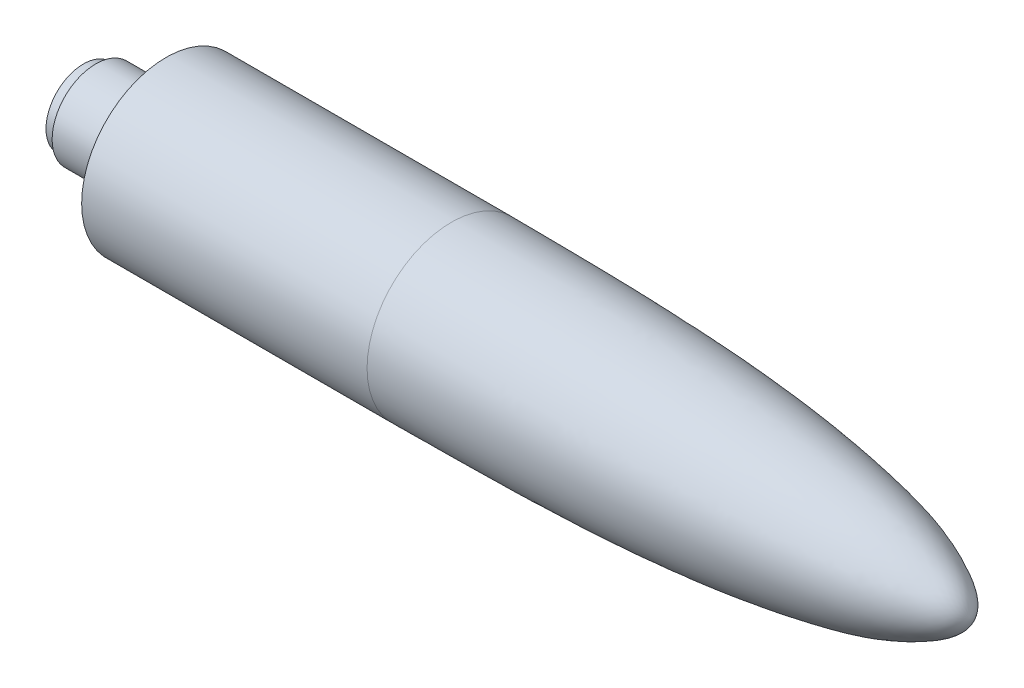
SolidWorks part; units mm, degrees
ref_plane "Front Plane" through (0, 0, 0) normal (0, 0, 1) x (1, 0, 0)
ref_plane "Top Plane" through (0, 0, 0) normal (0, 1, 0) x (1, 0, 0)
ref_plane "Right Plane" through (0, 0, 0) normal (1, 0, 0) x (0, 0, -1)
sketch "Sketch1" plane through (0, 0, 0) normal (0, 1, 0) x (1, 0, 0)
  line L0 (-27.2913, -6.7793) -> (4.4002, -6.7738) construction
  line L1 (0, 0) -> (57.2, 0) construction
  line L2 (0, 0) -> (0, -6)
  line L3 (0, -6) -> (20.3, -6)
  line L4 (0, 0) -> (0, 6) construction
  line L5 (0, 6) -> (20.3, 6) construction
  line L6 (57.2, 0) -> (57.0631, 6.2921) construction
  line L7 (0, 0) -> (57.2, 0)
  spline S0 degree 3 poles (20.3, -6) (29.6375, -5.9369) (42.0157, -5.942) (53.9398, -3.0181) (57.01, -1.0472) (57.2015, -0.0702) (57.2, 0) knots 0 0 0 0 0.749117 0.922481 0.994604 1 1 1 1
  dimension "D1" = 57.2
  dimension "D2" = 6
  dimension "D3" = 20.3
  dimension "D4" = 6
  dimension "D5" = 20.3
revolve "Revolve1" add sketch "Sketch1" angle 360 about L7
sketch "Sketch2" plane through (0, 0, 0) normal (-1, 0, 0) x (0, 0, 1)
  circle A0 centre (0, 0) radius 2.44
  dimension "D1" = 4.88
extrude "Boss-Extrude1" add sketch "Sketch2" along normal blind 1.5
sketch "Sketch3" plane through (-1.5, 0, 0) normal (-1, 0, 0) x (0, 0, 1)
  circle A0 centre (0, 0) radius 3.1
  dimension "D1" = 6.2
extrude "Boss-Extrude2" add sketch "Sketch3" along normal blind 3.5
sketch "Sketch4" plane through (-5, 0, 0) normal (-1, 0, 0) x (0, 0, 1)
  circle A0 centre (0, 0) radius 2.665
  dimension "D1" = 5.33
extrude "Boss-Extrude3" add sketch "Sketch4" along normal blind 0.87
sketch "Sketch5" plane through (0, 0, 0) normal (1, 0, 0) x (0, 0, -1)
  line L0 (0, 11.4415) -> (0, -8.9006) construction
  line L1 (-12.5624, 0) -> (12.5694, 0) construction
ref_plane "Plane1" through (57.2, 0, 0) normal (-1, 0, 0) x (0, 0, 1)
sketch "Sketch6" plane through (57.2, 0, 0) normal (-1, 0, 0) x (0, 0, 1)
  line L0 (0, 10.307) -> (0, -8.2808) construction
  line L1 (0, 11.4415) -> (0, -8.9006) construction
  line L2 (-7.2994, 0) -> (8.352, 0) construction
  line L3 (12.5624, 0) -> (-12.5694, 0) construction
  point P8 (0, 0)
